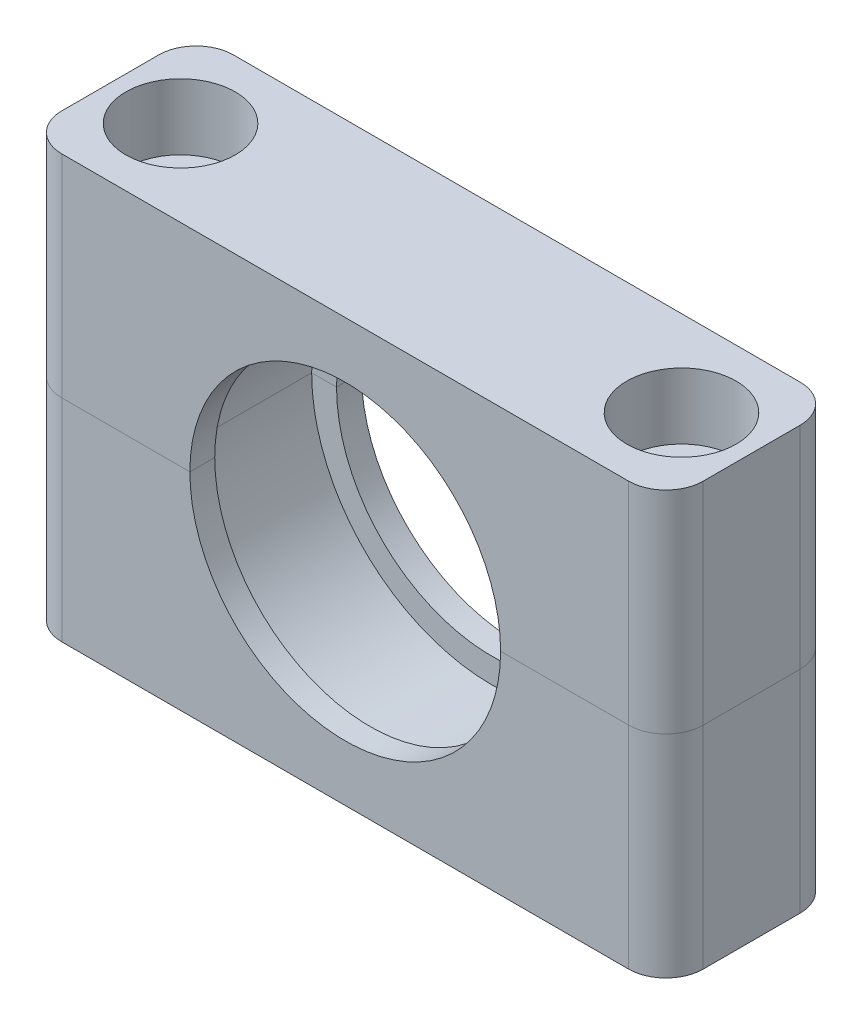
SolidWorks part; units mm, degrees
ref_plane "Front Plane" through (0, 0, 0) normal (0, 0, 1) x (1, 0, 0)
ref_plane "Top Plane" through (0, 0, 0) normal (0, 1, 0) x (1, 0, 0)
ref_plane "Right Plane" through (0, 0, 0) normal (1, 0, 0) x (0, 0, -1)
sketch "Sketch1" plane through (0, 0, 0) normal (0, 0, 1) x (1, 0, 0)
  circle A0 centre (0, 0) radius 14.5
  dimension "D1" = 29
extrude "Boss-Extrude1" add sketch "Sketch1" along normal blind 9.5
sketch "Sketch2" plane through (0, 0, 0) normal (0, 1, 0) x (1, 0, 0)
  line L0 (0, 0) -> (0, 4.3953) construction
  line L1 (-25.8, 2.15) -> (25.8, 2.15)
  line L2 (-25.8, 2.15) -> (-25.8, -11.65)
  line L3 (-25.8, -11.65) -> (25.8, -11.65)
  line L4 (25.8, 2.15) -> (25.8, -11.65)
  line L5 (14.5, 0) -> (-14.5, 0) construction
  line L6 (-14.5, -9.5) -> (14.5, -9.5) construction
  line L7 (-14.5, -4.75) -> (-25.8, -4.75) construction
  line L9 (-14.5, 0) -> (-14.5, -9.5) construction
  circle A0 centre (-20.15, -4.75) radius 2.65
  circle A1 centre (20.15, -4.75) radius 2.65
  point P7 (-25.8, -4.75)
  dimension "D3" = 5.3
  dimension "D1" = 2.15
  dimension "D2" = 2.15
  dimension "D4" = 3
extrude "Boss-Extrude2" add sketch "Sketch2" against normal blind 34 from offset 17 separate body
sketch "Sketch5" plane through (0, 0, 11.65) normal (0, 0, 1) x (1, 0, 0)
  circle A1 centre (0, 0) radius 14.5
  circle A2 centre (0, 0) radius 14.5
  dimension "D1" = 0
extrude "Cut-Extrude2" cut sketch "Sketch5" against normal through all both and the other way through all
sketch "Sketch6" plane through (0, 0, 11.65) normal (0, 0, 1) x (1, 0, 0)
  circle A0 centre (0, 0) radius 14.5
  circle A1 centre (0, 0) radius 12.5
  circle A2 centre (0, 0) radius 14.5 construction
  dimension "D1" = 25
extrude "Boss-Extrude4" add sketch "Sketch6" against normal blind 2
sketch "Sketch7" plane through (0, 0, -2.15) normal (0, 0, -1) x (-1, 0, 0)
  circle A0 centre (0, 0) radius 12.5 construction
  circle A1 centre (0, 0) radius 14.5
  circle A2 centre (0, 0) radius 14.5
  circle A3 centre (0, 0) radius 12.5
  dimension "D1" = 0
extrude "Boss-Extrude5" add sketch "Sketch7" against normal blind 2
ref_plane "Plane1" through (0, 0, 0) normal (0, 1, 0) x (1, 0, 0)
split "Split1" trim tools "Plane1" bodies to split 107 resulting bodies 108 109
sketch "Sketch8" plane through (0, 17, 0) normal (0, 1, 0) x (1, 0, 0)
  circle A0 centre (-20.15, -4.75) radius 4.4
  circle A1 centre (20.15, -4.75) radius 4.4
  dimension "D1" = 8.8
extrude "Cut-Extrude3" cut sketch "Sketch8" against normal blind 5.3 and the other way through all
fillet "Fillet1" radius 3 4 edges at (-25.8, 8.5, -2.15) (25.8, 8.5, -2.15) (25.8, 8.5, 11.65) (-25.8, 8.5, 11.65)
fillet "Fillet2" radius 3 4 edges at (25.8, -8.5, 11.65) (25.8, -8.5, -2.15) (-25.8, -8.5, -2.15) (-25.8, -8.5, 11.65)
